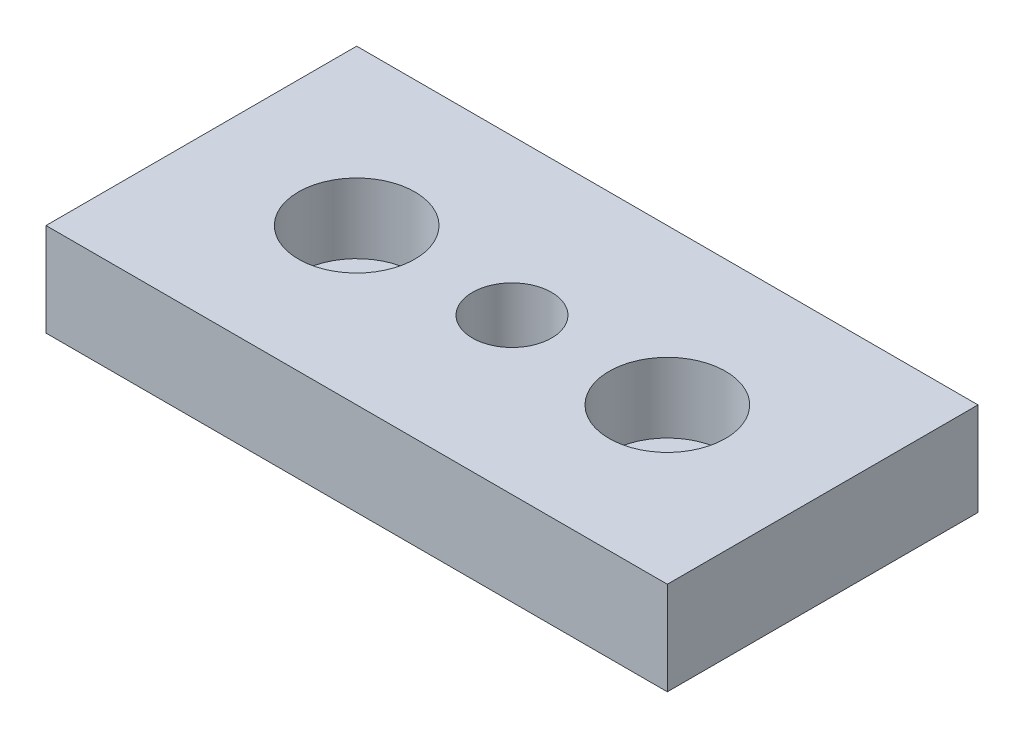
SolidWorks part; units mm, degrees
material "Алюминиевый сплав"
ref_plane "Спереди" through (0, 0, 0) normal (0, 0, 1) x (1, 0, 0)
ref_plane "Сверху" through (0, 0, 0) normal (0, 1, 0) x (1, 0, 0)
ref_plane "Справа" through (0, 0, 0) normal (1, 0, 0) x (0, 0, -1)
sketch "Эскиз1" plane through (0, 0, 0) normal (0, 1, 0) x (1, 0, 0)
  line L1 (-40, -20) -> (40, -20)
  line L2 (-40, -20) -> (-40, 20)
  line L3 (-40, 20) -> (40, 20)
  line L4 (40, -20) -> (40, 20)
  line L5 (-40, -20) -> (40, 20) construction
  line L6 (-40, 20) -> (40, -20) construction
  point P0 (0, 0)
  dimension "D1" = 80
  dimension "D2" = 40
extrude "Бобышка-Вытянуть1" add sketch "Эскиз1" along normal blind 12
sketch "Эскиз2" plane through (0, 0, 0) normal (0, 0, 1) x (1, 0, 0)
  line L0 (0, 0) -> (0, 12) construction
  line L1 (-40, 0) -> (40, 0) construction
  line L2 (-40, 12) -> (40, 12) construction
  line L3 (-27.5, 12) -> (-27.5, 3)
  line L4 (-27.5, 3) -> (-24.5, 3)
  line L5 (-24.5, 3) -> (-24.5, 0)
  line L6 (-24.5, 0) -> (-20, 0)
  line L7 (-20, 0) -> (-20, 12) construction
  line L8 (-20, 12) -> (-27.5, 12)
  line L9 (-20, 12) -> (-20, 0)
  dimension "D1" = 9
  dimension "D2" = 3
  dimension "D3" = 15
  dimension "D4" = 40
revolve "Вырез-Повернуть1" cut sketch "Эскиз2" angle 360 about L9
mirror "Зеркальное отражение1" about plane through (0, 0, 0) normal (1, 0, 0) of "Вырез-Повернуть1"
hole_wizard "Отверстие обработанное метчиком M121" positions "Эскиз3" profile "Эскиз5" tap size "M12" standard "ISO" end condition up to next
sketch "Эскиз3" plane through (0, 12, 0) normal (0, 1, 0) x (1, 0, 0)
  point P0 (0, 0)
sketch "Эскиз5" plane through (0, 12, 0) normal (1, 0, 0) x (0, 0, 1)
  line L0 (0, 0) -> (0, 12)
  line L1 (0, 12) -> (5.1, 12)
  line L2 (5.1, 12) -> (5.1, 0)
  line L5 (5.1, 0) -> (0, 0)
  line L11 (0, -6.35) -> (0, 107.95) construction
  dimension "Диаметр проходного сверла" = 10.2
  dimension "Глубина проходного сверла" = 12
cosmetic thread "Отверстие резьбы1" parameters "D2"=12
